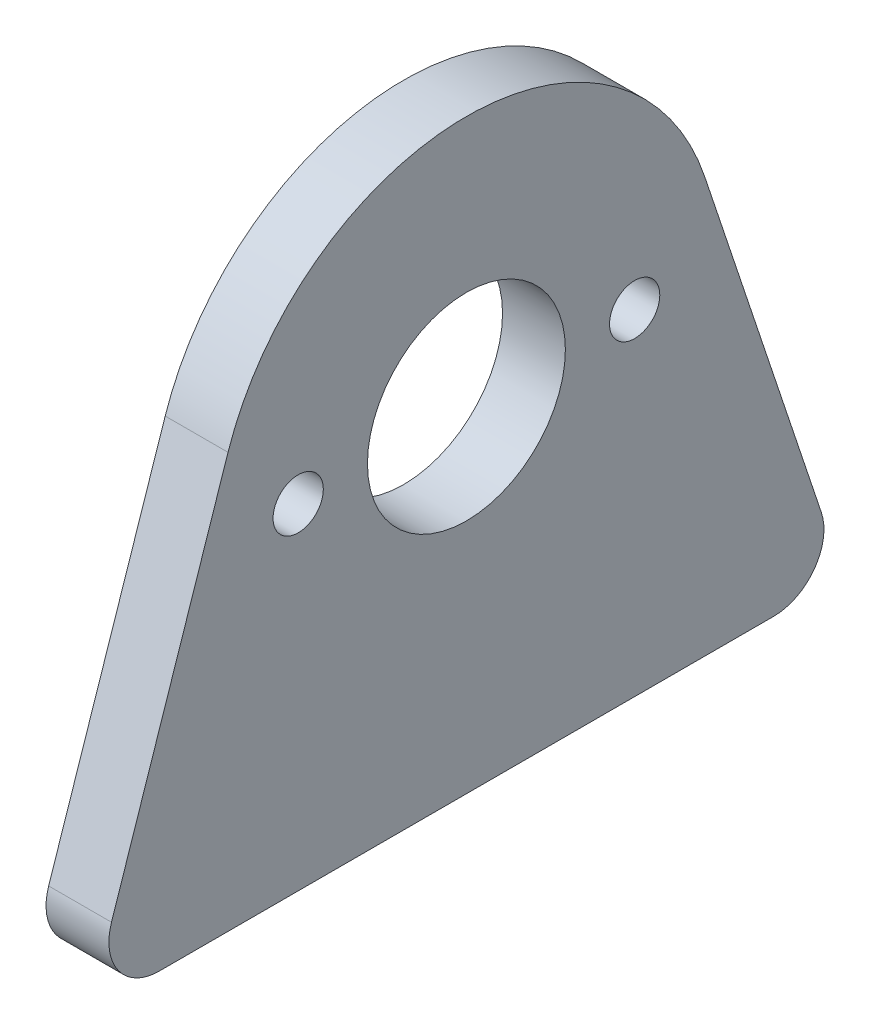
SolidWorks part; units mm, degrees
material "6061 Alloy"
ref_plane "Front Plane" through (0, 0, 0) normal (0, 0, 1) x (1, 0, 0)
ref_plane "Top Plane" through (0, 0, 0) normal (0, 1, 0) x (1, 0, 0)
ref_plane "Right Plane" through (0, 0, 0) normal (1, 0, 0) x (0, 0, -1)
sketch "Sketch1" plane through (0, 0, 0) normal (1, 0, 0) x (0, 0, -1)
  line L0 (0, 0) -> (-8.5, 0) construction
  line L1 (0, 0) -> (8.5, 0) construction
  line L2 (0, -5) -> (0, -16.938) construction
  line L3 (0, -16.938) -> (19.05, -16.938)
  line L4 (0, -16.938) -> (-19.05, -16.938)
  line L5 (-19.05, -16.938) -> (-12.0453, 4.0249)
  line L6 (19.05, -16.938) -> (12.0453, 4.0249)
  circle A0 centre (0, 0) radius 5
  circle A1 centre (-8.5, 0) radius 1.27
  circle A2 centre (8.5, 0) radius 1.27
  circle A3 centre (0, 0) radius 12.7
  dimension "D1" = 10
  dimension "D4" = 2.54
  dimension "D5" = 2.54
  dimension "D6" = 25.4
  dimension "D2" = 8.5
  dimension "D3" = 8.5
  dimension "D7" = 19.05
  dimension "D8" = 19.05
  dimension "D9" = 11.938
extrude "Boss-Extrude1" add sketch "Sketch1" against normal blind 3.175 contours A3 L5 L4 L3 L6 | A3 A0 A1 A2
fillet "Fillet1" radius 2.54 1 edges at (-1.5875, -16.938, -19.05)
fillet "Fillet2" radius 2.54 1 edges at (-1.5875, -16.938, 19.05)
